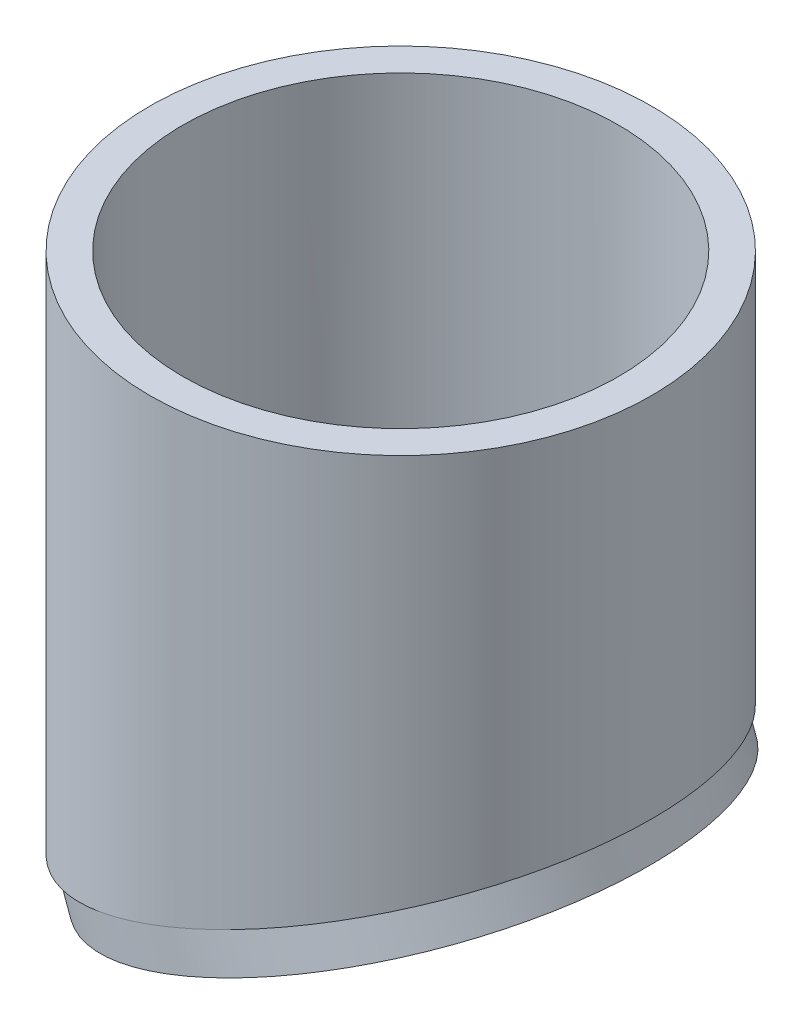
SolidWorks part; units mm, degrees
ref_plane "Front Plane" through (0, 0, 0) normal (0, 0, 1) x (1, 0, 0)
ref_plane "Top Plane" through (0, 0, 0) normal (0, 1, 0) x (1, 0, 0)
ref_plane "Right Plane" through (0, 0, 0) normal (1, 0, 0) x (0, 0, -1)
sketch "Sketch1" plane through (0, 0, 0) normal (0, 1, 0) x (1, 0, 0)
  circle A0 centre (0, 0) radius 72.5043
  circle A1 centre (0, 0) radius 83.4771
  dimension "D1" = 145.0086
  dimension "D2" = 166.9542
extrude "Boss-Extrude1" add sketch "Sketch1" along normal blind 152.4 and the other way blind 50.8
sketch "Sketch3" plane through (0, 0, 0) normal (0, 1, 0) x (1, 0, 0)
  line L0 (0, -127) -> (0, 0) construction
  line L1 (0, 0) -> (0, 127) construction
  dimension "D1" = 127
ref_plane "Plane2" through (0, 0, 0) normal (-0.342, 0.9397, 0) x (0, 0, -1)
sketch "Sketch4" plane through (0, 0, 0) normal (-0.342, 0.9397, 0) x (0, 0, -1)
  line L1 (101.6, -101.6) -> (-101.6, -101.6)
  line L2 (101.6, -101.6) -> (101.6, 101.6)
  line L3 (101.6, 101.6) -> (-101.6, 101.6)
  line L4 (-101.6, -101.6) -> (-101.6, 101.6)
  line L5 (101.6, -101.6) -> (-101.6, 101.6) construction
  line L6 (101.6, 101.6) -> (-101.6, -101.6) construction
  point P0 (0, 0)
  dimension "D1" = 203.2
  dimension "D2" = 203.2
extrude "Cut-Extrude1" cut sketch "Sketch4" against normal blind 152.4 contours L2 L3 L4 L1
sketch "Sketch5" plane through (0, 0, 0) normal (-0.342, 0.9397, 0) x (0, 0, -1)
  circle A0 centre (0, 0) radius 83.4771
  ellipse E2 centre (0, 0) end of major axis (0, -77.1575) minor radius 72.5043 construction
  ellipse E4 centre (0, 0) end of major axis (0, -77.1575) minor radius 72.5043
  dimension "D1" = 166.9542
extrude "Boss-Extrude3" add sketch "Sketch5" against normal blind 12.7
